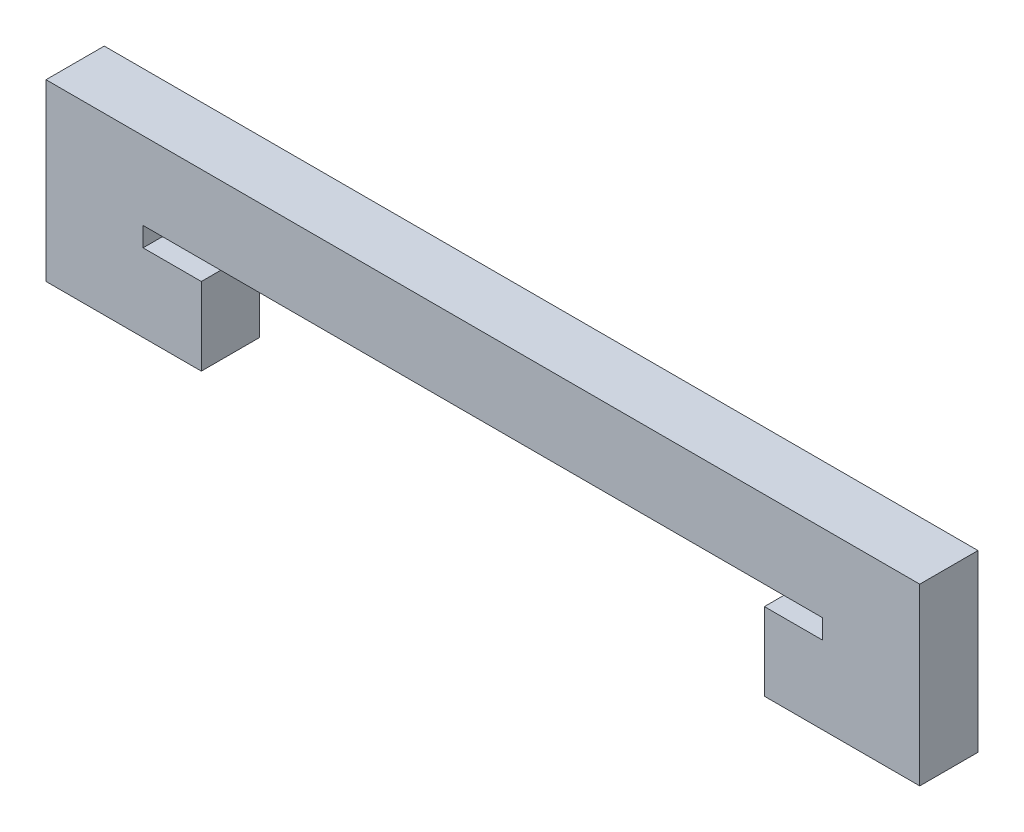
SolidWorks part; units mm, degrees
ref_plane "Płaszczyzna przednia" through (0, 0, 0) normal (0, 0, 1) x (1, 0, 0)
ref_plane "Płaszczyzna górna" through (0, 0, 0) normal (0, 1, 0) x (1, 0, 0)
ref_plane "Płaszczyzna prawa" through (0, 0, 0) normal (1, 0, 0) x (0, 0, -1)
sketch "Sketch2" plane through (0, 0, 0) normal (0, 0, 1) x (1, 0, 0)
  line L0 (0, 0) -> (17.5, 0) construction
  line L5 (0, 0) -> (-17.5, 0) construction
  line L7 (-17.5, 0) -> (-17.5, -1) construction
  line L8 (17.5, 0) -> (17.5, -1) construction
  line L9 (17.5, -1) -> (13.5, -1) construction
  line L10 (13.5, -1) -> (13.5, -7.5) construction
  line L11 (-17.5, -1) -> (-13.5, -1) construction
  line L12 (-13.5, -1) -> (-13.5, -7.5) construction
  line L13 (-13.5, -7.5) -> (13.5, -7.5) construction
  line L14 (-17.5, 0) -> (-17.5, -1) construction
  line L15 (-17.5, 0) -> (-17.5, -1)
  line L16 (-17.5, -1) -> (-14.5, -1)
  line L17 (-14.5, -1) -> (-14.5, -5)
  line L18 (-14.5, -5) -> (-22.5, -5)
  line L19 (-22.5, -5) -> (-22.5, 0)
  line L20 (-22.5, 0) -> (-22.5, 4)
  line L21 (-22.5, 4) -> (22.5, 4)
  line L22 (22.5, 4) -> (22.5, -5)
  line L23 (22.5, -5) -> (14.5, -5)
  line L24 (14.5, -5) -> (14.5, -1)
  line L25 (14.5, -1) -> (17.5, -1)
  line L26 (17.5, -1) -> (17.5, 0)
  line L27 (17.5, 0) -> (-17.5, 0)
  point P10 (-22.5, 0)
  point P11 (-22.5, -5)
  point P12 (-14.5, -5)
  point P13 (-22.5, 0)
  point P14 (-22.5, 4)
  point P16 (-14.5, -1)
  point P17 (-17.5, -1)
  point P18 (-17.5, 0)
  dimension "D1" = 5
  dimension "D2" = 5
  dimension "D3" = 8
  dimension "D4" = 4
  dimension "D5" = 0
  dimension "D6" = 0
  dimension "D7" = 35
  dimension "D8" = 1
  dimension "D9" = 4
  dimension "D10" = 4
  dimension "D11" = 1
  dimension "D12" = 27
  dimension "D13" = 6.5
  dimension "D14" = 6.5
  dimension "D16" = 3
  dimension "D17" = 1
  dimension "D18" = 9
  dimension "D19" = 9
  dimension "D20" = 8
  dimension "D21" = 1
  dimension "D22" = 0
  dimension "D23" = 0
  dimension "D25" = 45
extrude "Boss-Extrude1" add sketch "Sketch2" along normal blind 3
